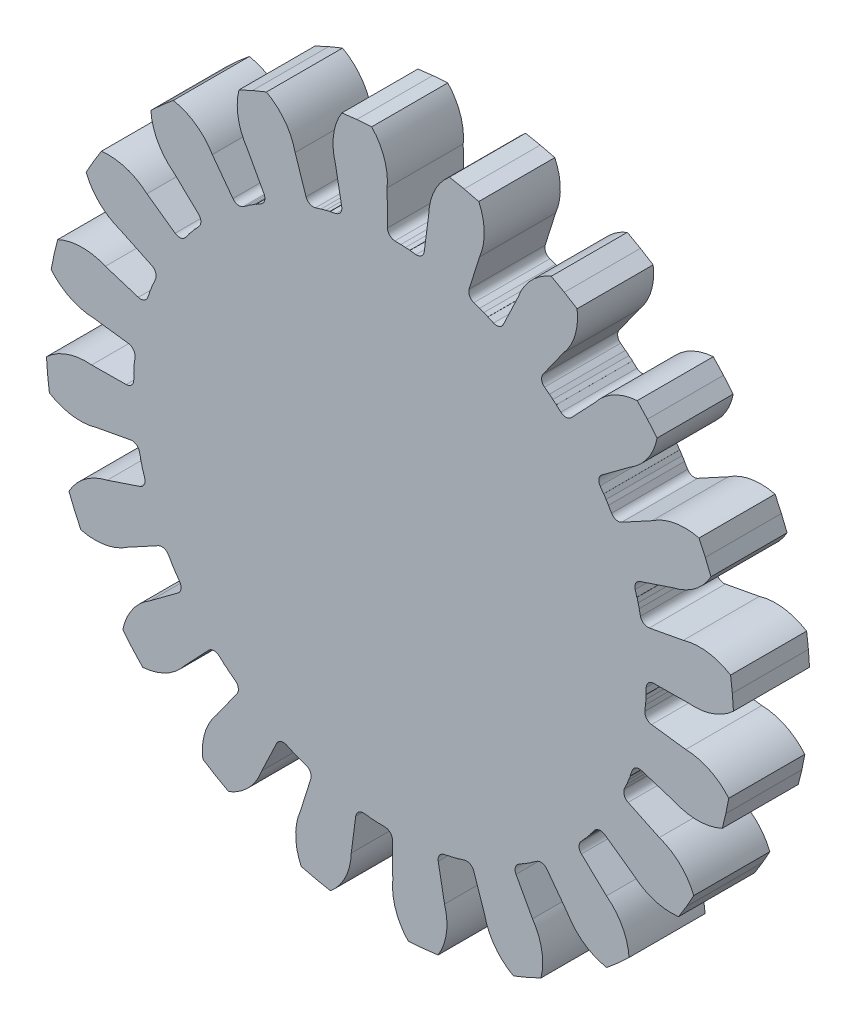
SolidWorks part; units mm, degrees
ref_plane "Front Plane" through (0, 0, 0) normal (0, 0, 1) x (1, 0, 0)
ref_plane "Top Plane" through (0, 0, 0) normal (0, 1, 0) x (1, 0, 0)
ref_plane "Right Plane" through (0, 0, 0) normal (1, 0, 0) x (0, 0, -1)
sketch "Sketch1" plane through (0, 0, 0) normal (0, 0, 1) x (1, 0, 0)
  line L0 (0, 0) -> (50.0804, -2.1514) construction
  line L1 (0, 0) -> (49.3587, -10.9062) construction
  line L2 (0, 0) -> (49.9745, -6.5436) construction
  line L3 (0, 0) -> (48.3952, -8.4984) construction
  line L4 (38.8859, -5.0917) -> (33.4324, -4.3776)
  line L5 (33.4324, -4.3776) -> (33.6868, -1.4471)
  line L6 (33.6868, -1.4471) -> (0, 0)
  line L7 (44.5364, -7.8208) -> (44.1528, -9.756)
  line L8 (31.1602, -12.8814) -> (0, 0)
  line L9 (32.1644, -10.1166) -> (31.1602, -12.8814)
  line L10 (37.411, -11.7668) -> (32.1644, -10.1166)
  line L11 (43.6853, -11.6726) -> (44.1528, -9.756)
  circle A0 centre (0, 0) radius 45.2178 construction
  circle A1 centre (0, 0) radius 39.2178 construction
  circle A2 centre (0, 0) radius 33.7178 construction
  arc A3 (44.5364, -7.8208) -> (38.8859, -5.0917) centre (38.6825, -12.7269) ccw
  arc A4 (43.6853, -11.6726) -> (37.411, -11.7668) centre (40.4436, -4.7567) cw
  point P5 (38.2941, -8.4614)
  point P10 (33.4324, -4.3776)
  point P11 (38.6268, -6.783)
  point P12 (44.8351, -5.8707)
  point P13 (39.1817, -1.6832)
  dimension "D1" = 11.5
  dimension "D2" = 5.5
  dimension "D3" = 10
  dimension "D4" = 5
  dimension "D5" = 2.5
extrude "Boss-Extrude1" add sketch "Sketch1" along normal blind 10
fillet "Fillet2" radius 1 2 edges at (32.1644, -10.1166, 5) (33.4324, -4.3776, 5)
pattern_circular "CirPattern1" count 20 over 360 about axis through (0, 0, 0) along (0, 0, 1) of "Boss-Extrude1", "Fillet2"
